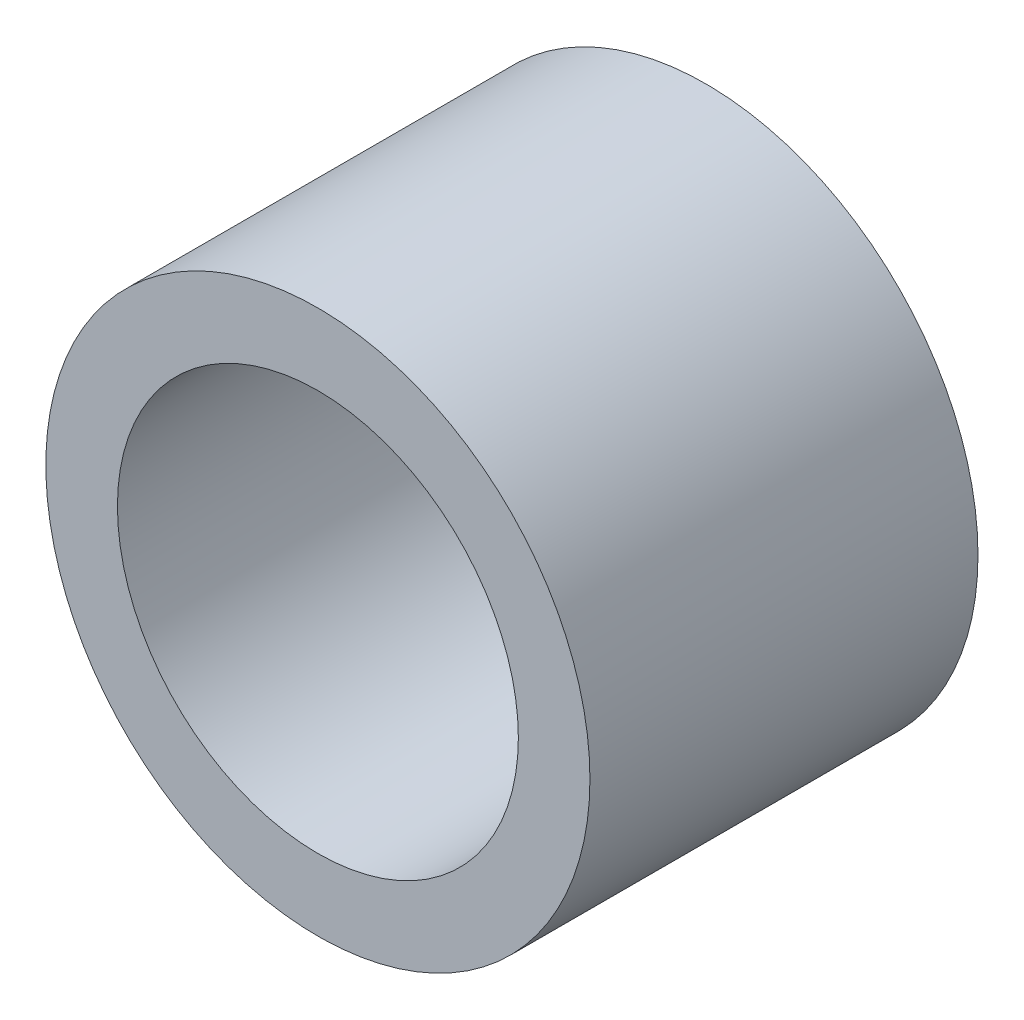
SolidWorks part; units mm, degrees
ref_plane "Front Plane" through (0, 0, 0) normal (0, 0, 1) x (1, 0, 0)
ref_plane "Top Plane" through (0, 0, 0) normal (0, 1, 0) x (1, 0, 0)
ref_plane "Right Plane" through (0, 0, 0) normal (1, 0, 0) x (0, 0, -1)
sketch "Sketch1" plane through (0, 0, 0) normal (0, 0, 1) x (1, 0, 0)
  circle A0 centre (0, 0) radius 4.826
  circle A1 centre (0, 0) radius 3.556
  dimension "D1" = 7.112
  dimension "D2" = 1.27
extrude "Boss-Extrude1" add sketch "Sketch1" along normal blind 6.8834
